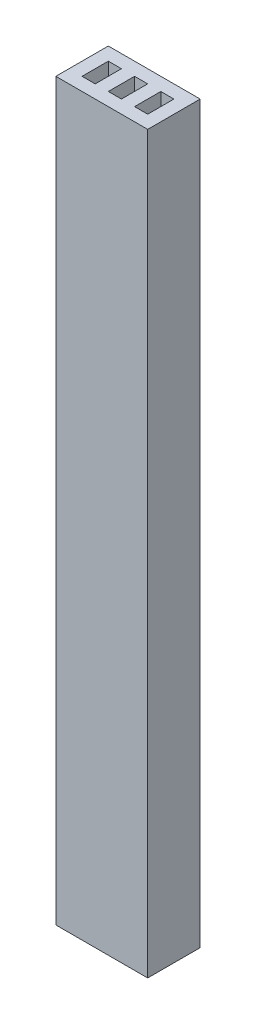
SolidWorks part; units mm, degrees
ref_plane "Front Plane" through (0, 0, 0) normal (0, 0, 1) x (1, 0, 0)
ref_plane "Top Plane" through (0, 0, 0) normal (0, 1, 0) x (1, 0, 0)
ref_plane "Right Plane" through (0, 0, 0) normal (1, 0, 0) x (0, 0, -1)
sketch "Sketch1" plane through (0, 0, 0) normal (0, 1, 0) x (1, 0, 0)
  line L0 (-4.8161, -3.7634) -> (-3.8161, -3.7634) construction
  line L1 (-5.8161, -3.7634) -> (-4.8161, -3.7634)
  line L2 (-5.8161, -3.7634) -> (-5.8161, -1.7634)
  line L3 (-5.8161, -1.7634) -> (-4.8161, -1.7634)
  line L4 (-4.8161, -3.7634) -> (-4.8161, -1.7634)
  line L5 (-2.8161, -3.7634) -> (-1.8161, -3.7634) construction
  line L6 (-3.8161, -3.7634) -> (-2.8161, -3.7634)
  line L7 (-3.8161, -3.7634) -> (-3.8161, -1.7634)
  line L8 (-3.8161, -1.7634) -> (-2.8161, -1.7634)
  line L9 (-2.8161, -3.7634) -> (-2.8161, -1.7634)
  line L10 (-0.8161, -3.7634) -> (0.1839, -3.7634) construction
  line L11 (-1.8161, -3.7634) -> (-0.8161, -3.7634)
  line L12 (-1.8161, -3.7634) -> (-1.8161, -1.7634)
  line L13 (-1.8161, -1.7634) -> (-0.8161, -1.7634)
  line L14 (-0.8161, -3.7634) -> (-0.8161, -1.7634)
  line L15 (0.1839, -3.7634) -> (0.1839, -4.7634) construction
  line L16 (-5.8161, -1.7634) -> (-5.8161, -0.7634) construction
  line L17 (-5.8161, -0.7634) -> (-6.8161, -0.7634) construction
  line L18 (-6.8161, -0.7634) -> (0.1839, -0.7634)
  line L19 (-6.8161, -0.7634) -> (-6.8161, -4.7634)
  line L20 (-6.8161, -4.7634) -> (0.1839, -4.7634)
  line L21 (0.1839, -0.7634) -> (0.1839, -4.7634)
extrude "Boss-Extrude1" add sketch "Sketch1" along normal blind 56
